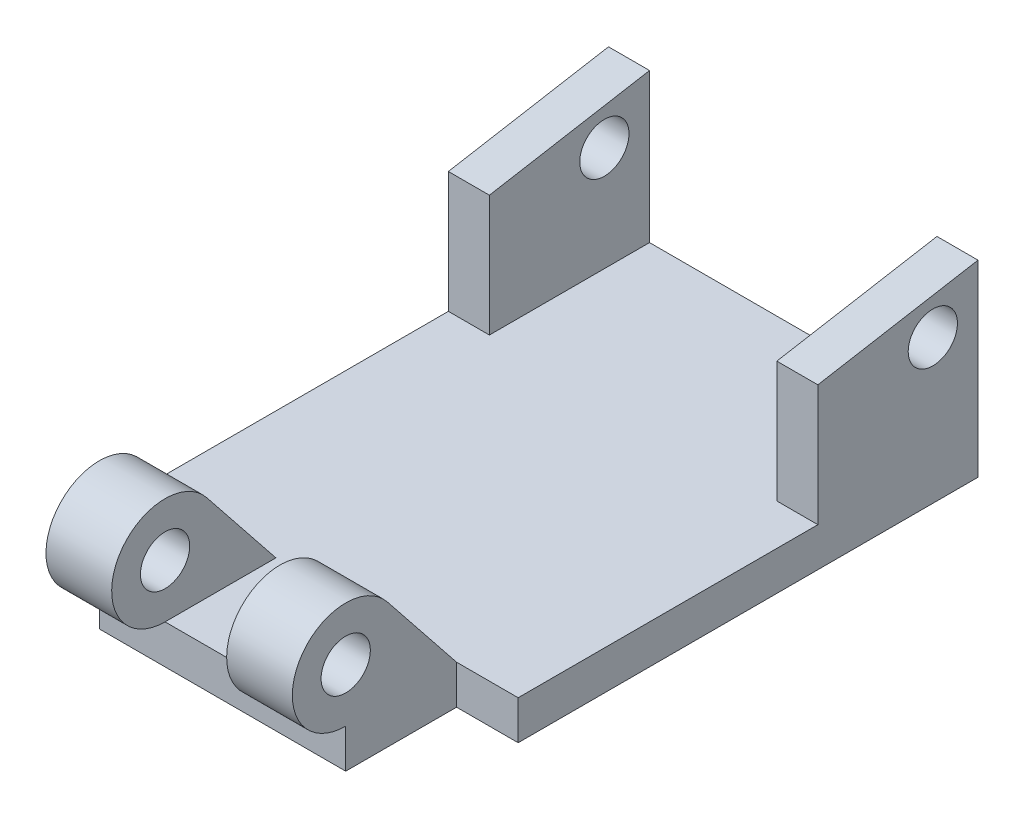
SolidWorks part; units mm, degrees
material "6061-T6 (SS)"
ref_plane "Front Plane" through (0, 0, 0) normal (0, 0, 1) x (1, 0, 0)
ref_plane "Top Plane" through (0, 0, 0) normal (0, 1, 0) x (1, 0, 0)
ref_plane "Right Plane" through (0, 0, 0) normal (1, 0, 0) x (0, 0, -1)
sketch "Sketch1" plane through (0, 0, 0) normal (0, 1, 0) x (1, 0, 0)
  line L1 (0, 0) -> (57.15, 0)
  line L2 (0, 0) -> (0, 71.12)
  line L3 (0, 71.12) -> (57.15, 71.12)
  line L4 (57.15, 0) -> (57.15, 71.12)
  line L5 (9.525, 0) -> (47.625, 0)
  line L6 (9.525, 0) -> (9.525, -17.145)
  line L7 (9.525, -17.145) -> (47.625, -17.145)
  line L8 (47.625, 0) -> (47.625, -17.145)
  dimension "D1" = 57.15
  dimension "D2" = 71.12
  dimension "D3" = 88.265
  dimension "D4" = 38.1
  dimension "D5" = 9.525
extrude "Boss-Extrude1" add sketch "Sketch1" along normal blind 6.0325 contours L1 L4 L3 L2 | L8 L1 L6 L7
sketch "Sketch2" plane through (9.525, 0, 0) normal (-1, 0, 0) x (0, 0, 1)
  line L0 (0, 6.0325) -> (10.6918, 19.4354)
  line L2 (0, 6.0325) -> (17.145, 6.0325) construction
  circle A1 centre (17.145, 14.2875) radius 8.255
  circle A2 centre (17.145, 14.2875) radius 3.81
  line M5 (17.145, 6.0325) -> (0, 6.0325)
  dimension "D1" = 4.445
  dimension "D2" = 7.62
extrude "Boss-Extrude2" add sketch "Sketch2" against normal up to surface (38.1 mm away) contours A1 L0 M5 | A1 A2 up to face at (47.625, 3.0162, 8.5725)
sketch "Sketch3" plane through (0, 6.0325, 0) normal (0, 1, 0) x (1, 0, 0)
  line L0 (47.625, 0) -> (9.525, 0) construction
  line L1 (9.525, 0) -> (19.685, 0)
  line L2 (9.525, 0) -> (9.525, -25.4)
  line L3 (9.525, -25.4) -> (19.685, -25.4)
  line L4 (19.685, 0) -> (19.685, -25.4)
  line L5 (9.525, -25.4) -> (47.625, -25.4) construction
  line L8 (47.625, 0) -> (37.465, 0)
  line L9 (47.625, 0) -> (47.625, -25.4)
  line L10 (47.625, -25.4) -> (37.465, -25.4)
  line L11 (37.465, 0) -> (37.465, -25.4)
  line L12 (19.685, 0) -> (37.465, 0)
  line L13 (19.685, 0) -> (19.685, -25.4)
  line L14 (19.685, -25.4) -> (37.465, -25.4)
  line L15 (37.465, 0) -> (37.465, -25.4)
  line M8 (9.525, 0) -> (47.625, 0)
  dimension "D1" = 10.16
  dimension "D2" = 10.16
extrude "Cut-Extrude1" cut sketch "Sketch3" along normal blind 35.7505 contours L4 L14 L11 M8
sketch "Sketch4" plane through (0, 0, 0) normal (-1, 0, 0) x (0, 0, 1)
  line L0 (-46.355, 6.0325) -> (-46.355, 24.765)
  line L1 (0, 6.0325) -> (-71.12, 6.0325) construction
  line L2 (-46.355, 24.765) -> (-71.12, 29.083)
  line L3 (-71.12, 29.083) -> (-71.12, 6.0325)
  line L4 (-71.12, 6.0325) -> (-46.355, 6.0325)
  line L5 (0, 0) -> (-71.12, 0) construction
  circle A0 centre (-64.135, 22.225) radius 3.81
  dimension "D6" = 7.62
  dimension "D1" = 24.765
  dimension "D2" = 29.083
  dimension "D3" = 24.765
  dimension "D4" = 22.225
  dimension "D5" = 6.985
extrude "Boss-Extrude3" add sketch "Sketch4" against normal up to surface (57.15 mm away) up to face at (57.15, 3.0162, -35.56)
sketch "Sketch5" plane through (0, 0, -71.12) normal (0, 0, -1) x (-1, 0, 0)
  line L0 (-57.15, 6.0325) -> (0, 6.0325) construction
  line L1 (-57.15, 6.0325) -> (0, 6.0325)
  line L2 (-57.15, 29.083) -> (0, 29.083) construction
  line L3 (-57.15, 6.0325) -> (-50.8, 6.0325)
  line L4 (-57.15, 6.0325) -> (-57.15, 29.083)
  line L5 (-57.15, 29.083) -> (-50.8, 29.083)
  line L6 (-50.8, 6.0325) -> (-50.8, 29.083)
  line L7 (-50.8, 29.083) -> (-6.35, 29.083)
  line L8 (0, 6.0325) -> (-6.35, 6.0325)
  line L9 (0, 6.0325) -> (0, 29.083)
  line L10 (0, 29.083) -> (-6.35, 29.083)
  line L11 (-6.35, 6.0325) -> (-6.35, 29.083)
  line M7 (0, 29.083) -> (-57.15, 29.083)
  dimension "D1" = 6.35
  dimension "D2" = 6.35
extrude "Cut-Extrude2" cut sketch "Sketch5" against normal blind 35.7505 contours L1 L11 L6 M7
